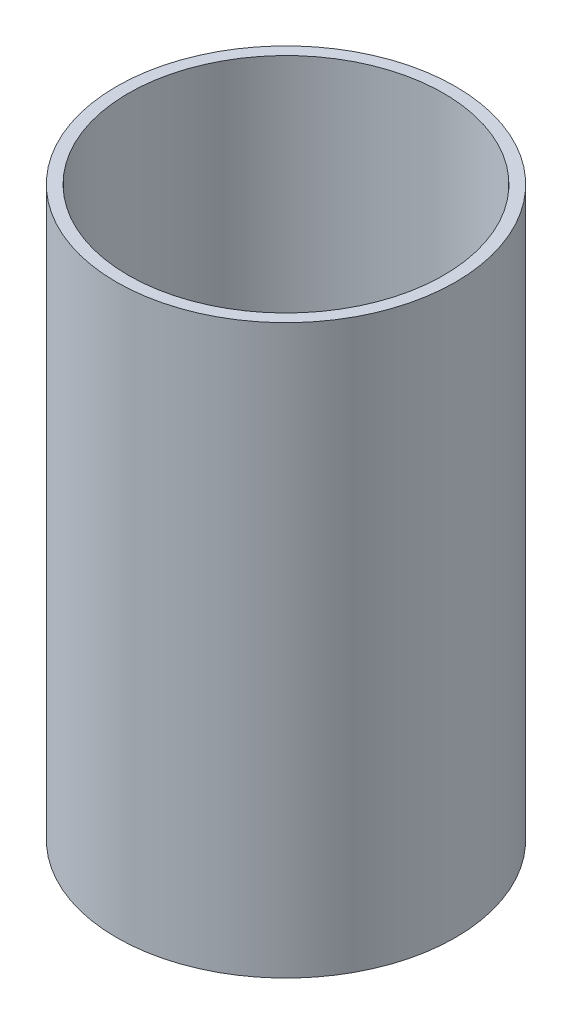
SolidWorks part; units mm, degrees
material "Thornel Mat VMA"
ref_plane "Front Plane" through (0, 0, 0) normal (0, 0, 1) x (1, 0, 0)
ref_plane "Top Plane" through (0, 0, 0) normal (0, 1, 0) x (1, 0, 0)
ref_plane "Right Plane" through (0, 0, 0) normal (1, 0, 0) x (0, 0, -1)
sketch "Sketch1" plane through (0, 0, 0) normal (0, 1, 0) x (1, 0, 0)
  circle A0 centre (0, 0) radius 25.4
  circle A1 centre (0, 0) radius 27.305
  dimension "D1" = 54.61
  dimension "D2" = 50.8
extrude "Boss-Extrude1" add sketch "Sketch1" along normal blind 91.44
